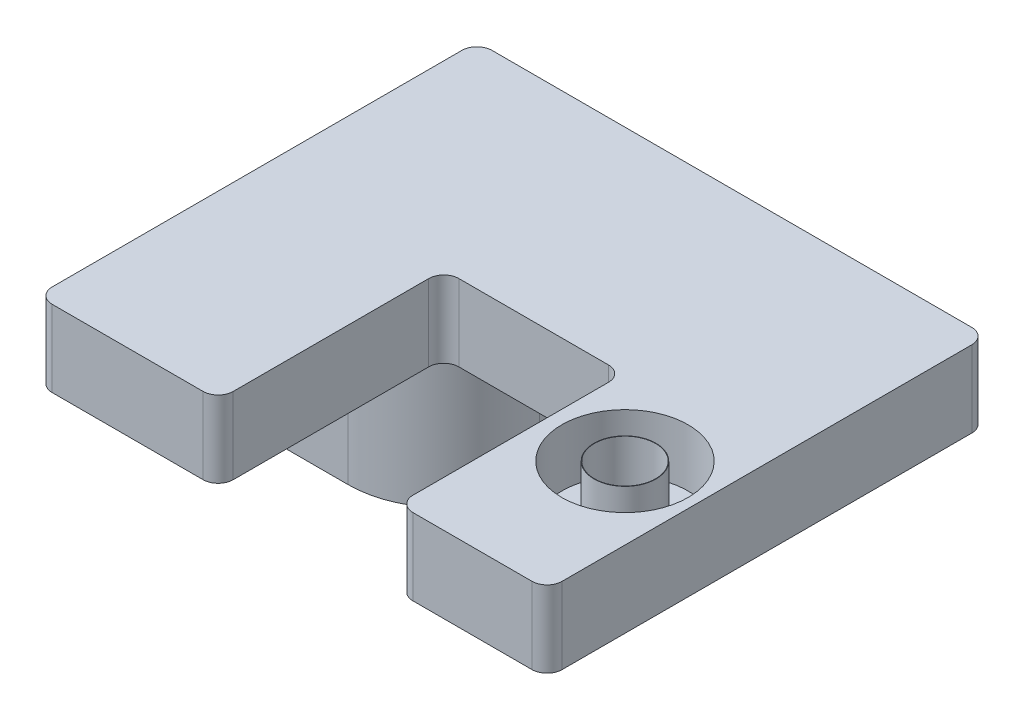
SolidWorks part; units mm, degrees
ref_plane "Front Plane" through (0, 0, 0) normal (0, 0, 1) x (1, 0, 0)
ref_plane "Top Plane" through (0, 0, 0) normal (0, 1, 0) x (1, 0, 0)
ref_plane "Right Plane" through (0, 0, 0) normal (1, 0, 0) x (0, 0, -1)
sketch "Sketch1" plane through (0, 0, 0) normal (0, 1, 0) x (1, 0, 0)
  line L1 (0, 0) -> (33.8667, 0)
  line L2 (0, 0) -> (0, 29.21)
  line L3 (0, 29.21) -> (33.8667, 29.21)
  line L4 (33.8667, 0) -> (33.8667, 29.21)
  line L5 (12.0227, 0) -> (23.9607, 0)
  line L6 (12.0227, 0) -> (12.0227, 14.986)
  line L7 (12.0227, 14.986) -> (23.9607, 14.986)
  line L8 (23.9607, 0) -> (23.9607, 14.986)
  circle A0 centre (29.0407, 10) radius 2.032
  dimension "D8" = 4.064
  dimension "D1" = 33.8667
  dimension "D2" = 29.21
  dimension "D3" = 9.906
  dimension "D4" = 11.938
  dimension "D5" = 5.08
  dimension "D6" = 14.986
  dimension "D7" = 10
extrude "Boss-Extrude1" add sketch "Sketch1" along normal blind 5.08 contours L8 L1 L4 L3 L2 L6 L7 A0
fillet "Fillet2" radius 1 8 edges at (0, 2.54, 0) (0, 2.54, -29.21) (33.8667, 2.54, -29.21) (33.8667, 2.54, 0) (23.9607, 2.54, 0) (23.9607, 2.54, -14.986) (12.0227, 2.54, -14.986) (12.0227, 2.54, 0)
sketch "Sketch4" plane through (0, 5.08, 0) normal (0, 1, 0) x (1, 0, 0)
  circle A0 centre (29.0407, 10) radius 4.191
  circle A1 centre (29.0407, 10) radius 2.032 construction
  dimension "D1" = 8.382
extrude "Cut-Extrude3" cut sketch "Sketch4" against normal offset from surface (3.81 mm away) 1.27 up to face at (29.0407, 0, -7.968)
sketch "Sketch5" plane through (0, 1.27, 0) normal (0, 1, 0) x (1, 0, 0)
  circle A0 centre (29.0407, 10) radius 2.032
  circle A1 centre (29.0407, 10) radius 2.032 construction
  circle A2 centre (29.0407, 10) radius 2.0574
  dimension "D1" = 0.0254
extrude "Boss-Extrude2" add sketch "Sketch5" along normal up to surface (3.81 mm away) up to face at (29.0407, 5.08, -5.809)
sketch "Sketch6" plane through (0, 0, 0) normal (0, -1, 0) x (1, 0, 0)
  line L0 (1, -29.21) -> (12.3156, -29.21)
  line L1 (1, -29.21) -> (32.8667, -29.21) construction
  line L2 (12.3156, -29.21) -> (12.3156, -21.0431)
  line L3 (5.9656, -14.6931) -> (0, -14.6931)
  line L4 (0, -1) -> (0, -28.21) construction
  line L5 (0, -14.6931) -> (0, -28.21)
  arc A0 (0, -28.21) -> (1, -29.21) centre (1, -28.21) ccw construction
  arc A1 (1, -29.21) -> (0, -28.21) centre (1, -28.21) cw
  arc A2 (12.0227, -13.986) -> (13.0227, -14.986) centre (13.0227, -13.986) ccw construction
  arc A3 (12.3156, -21.0431) -> (5.9656, -14.6931) centre (5.9656, -21.0431) ccw
  point P19 (12.3156, -14.6931)
  dimension "D1" = 6.35
extrude "Boss-Extrude3" add sketch "Sketch6" along normal blind 10.16
